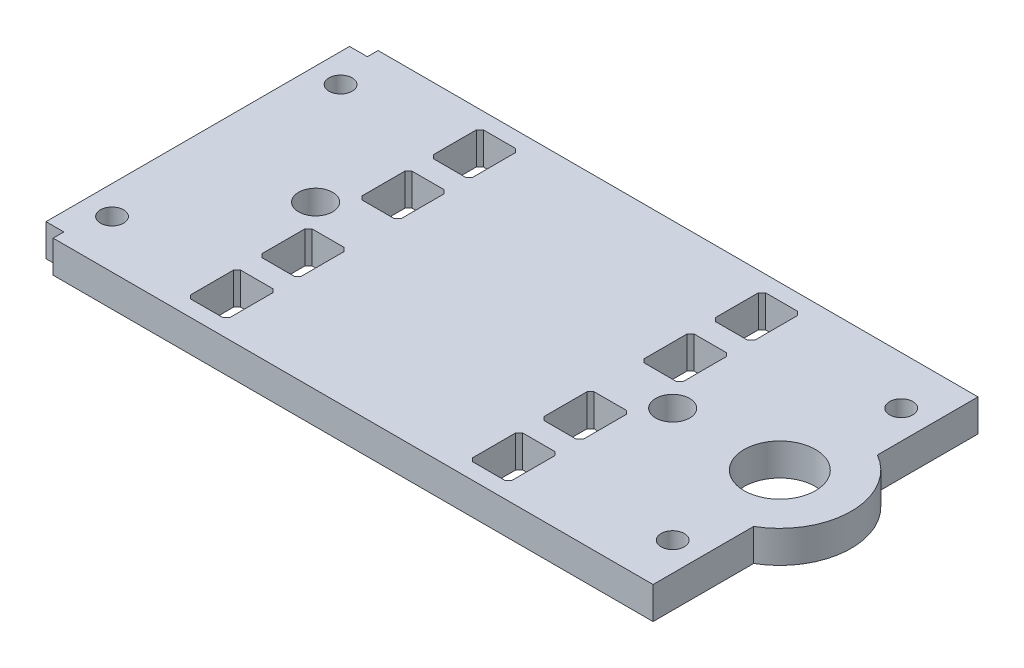
SolidWorks part; units mm, degrees
ref_plane "Front Plane" through (0, 0, 0) normal (0, 0, 1) x (1, 0, 0)
ref_plane "Top Plane" through (0, 0, 0) normal (0, 1, 0) x (1, 0, 0)
ref_plane "Right Plane" through (0, 0, 0) normal (1, 0, 0) x (0, 0, -1)
sketch "Sketch2" plane through (0, 0, 0) normal (0, 1, 0) x (1, 0, 0)
  line L0 (0, 0) -> (45, 0) construction
  line L1 (-41.5, -22.75) -> (45, -22.75)
  line L2 (-41.5, -22.75) -> (-41.5, 22.75)
  line L3 (-41.5, 22.75) -> (45, 22.75)
  line L4 (45, -22.75) -> (45, 22.75)
  dimension "D1" = 22.75
  dimension "D2" = 41.5
  dimension "D3" = 45
  dimension "D4" = 22.75
extrude "Boss-Extrude1" add sketch "Sketch2" along normal blind 4.5
sketch "Sketch3" plane through (0, 4.5, 0) normal (0, 1, 0) x (1, 0, 0)
  line L1 (-37.5, -16) -> (41, -16) construction
  line L2 (-37.5, -16) -> (-37.5, 16) construction
  line L3 (-37.5, 16) -> (41, 16) construction
  line L4 (41, -16) -> (41, 16) construction
  line L8 (-25, 0) -> (25, 0) construction
  line L9 (0, 0) -> (0, 16) construction
  line L10 (0, 0) -> (0, -16) construction
  circle A0 centre (-37.5, -16) radius 1.625
  circle A1 centre (-37.5, 16) radius 1.625
  circle A2 centre (41, 16) radius 1.625
  circle A3 centre (41, -16) radius 1.625
  circle A4 centre (25, 0) radius 2.3813
  circle A5 centre (-25, 0) radius 2.3813
  dimension "D5" = 3.25
  dimension "D6" = 4.7625
  dimension "D1" = 16
  dimension "D2" = 37.5
  dimension "D3" = 41
  dimension "D7" = 50
extrude "Cut-Extrude1" cut sketch "Sketch3" against normal through all
sketch "Sketch4" plane through (0, 4.5, 0) normal (0, 1, 0) x (1, 0, 0)
  line L0 (-17, -3.5) -> (-17, 3.5) construction
  line L1 (-22.5, 10.5) -> (-17, 10.5)
  line L2 (-22.5, 10.5) -> (-22.5, 3.5)
  line L3 (-22.5, 3.5) -> (-17, 3.5)
  line L4 (-17, 10.5) -> (-17, 3.5)
  line L5 (-22.5, -3.5) -> (-17, -3.5)
  line L6 (-22.5, -3.5) -> (-22.5, -10.5)
  line L7 (-22.5, -10.5) -> (-17, -10.5)
  line L8 (-17, -3.5) -> (-17, -10.5)
  line L9 (-22.5, 20.5) -> (-17, 20.5)
  line L10 (-22.5, 20.5) -> (-22.5, 13.5)
  line L11 (-22.5, 13.5) -> (-17, 13.5)
  line L12 (-17, 20.5) -> (-17, 13.5)
  line L13 (-22.5, -13.5) -> (-17, -13.5)
  line L14 (-22.5, -13.5) -> (-22.5, -20.5)
  line L15 (-22.5, -20.5) -> (-17, -20.5)
  line L16 (-17, -13.5) -> (-17, -20.5)
  line L17 (-17, 0) -> (0, 0) construction
  line L18 (-17, 7) -> (-13.5084, 7) construction
  line L19 (-17, 17) -> (-13.0676, 17) construction
  line L20 (-17, 10.5) -> (-17, 13.5) construction
  line L21 (-17, -13.5) -> (-17, -10.5) construction
  dimension "D1" = 17
  dimension "D2" = 22.5
  dimension "D3" = 7
  dimension "D4" = 17
  dimension "D5" = 7
  dimension "D6" = 7
extrude "Cut-Extrude2" cut sketch "Sketch4" against normal through all
mirror "Mirror1" about plane through (0, 0, 0) normal (1, 0, 0) of "Cut-Extrude2"
chamfer "Chamfer1" distance 0.5 angle 45 32 edges at (17, 2.25, -20.5) (17, 2.25, -10.5) (17, 2.25, 3.5) (17, 2.25, 13.5) (-22.5, 2.25, 13.5) (-22.5, 2.25, 3.5) (-22.5, 2.25, -10.5) (-22.5, 2.25, -20.5) (-17, 2.25, -20.5) (-17, 2.25, -10.5) (-17, 2.25, 3.5) (-17, 2.25, 13.5) (22.5, 2.25, 13.5) (22.5, 2.25, 3.5) (22.5, 2.25, -10.5) (22.5, 2.25, -20.5) (22.5, 2.25, -13.5) (22.5, 2.25, -3.5) (22.5, 2.25, 10.5) (22.5, 2.25, 20.5) (-17, 2.25, 20.5) (-17, 2.25, 10.5) (-17, 2.25, -3.5) (-17, 2.25, -13.5) (17, 2.25, -13.5) (17, 2.25, -3.5) (17, 2.25, 10.5) (17, 2.25, 20.5) (-22.5, 2.25, 20.5) (-22.5, 2.25, 10.5) (-22.5, 2.25, -3.5) (-22.5, 2.25, -13.5)
sketch "Sketch5" plane through (0, 4.5, 0) normal (0, 1, 0) x (1, 0, 0)
  line L0 (40, 0) -> (0, 0) construction
  circle A0 centre (40, 0) radius 10
  dimension "D2" = 20
  dimension "D1" = 40
extrude "Boss-Extrude2" add sketch "Sketch5" against normal up to surface (4.5 mm away) up to face at (19.75, 0, -17)
sketch "Sketch6" plane through (0, 4.5, 0) normal (0, 1, 0) x (1, 0, 0)
  line L1 (-41.5, -22.75) -> (-39, -22.75)
  line L2 (-41.5, -22.75) -> (-41.5, -21.25)
  line L3 (-41.5, -21.25) -> (-39, -21.25)
  line L4 (-39, -22.75) -> (-39, -21.25)
  line L5 (-41.5, 22.75) -> (-39, 22.75)
  line L6 (-41.5, 22.75) -> (-41.5, 21.25)
  line L7 (-41.5, 21.25) -> (-39, 21.25)
  line L8 (-39, 22.75) -> (-39, 21.25)
  circle A0 centre (40, 0) radius 5
  arc A1 (45, -8.6603) -> (45, 8.6603) centre (40, 0) ccw construction
  dimension "D1" = 10
  dimension "D2" = 2.5
  dimension "D3" = 1.5
extrude "Cut-Extrude3" cut sketch "Sketch6" against normal through all
